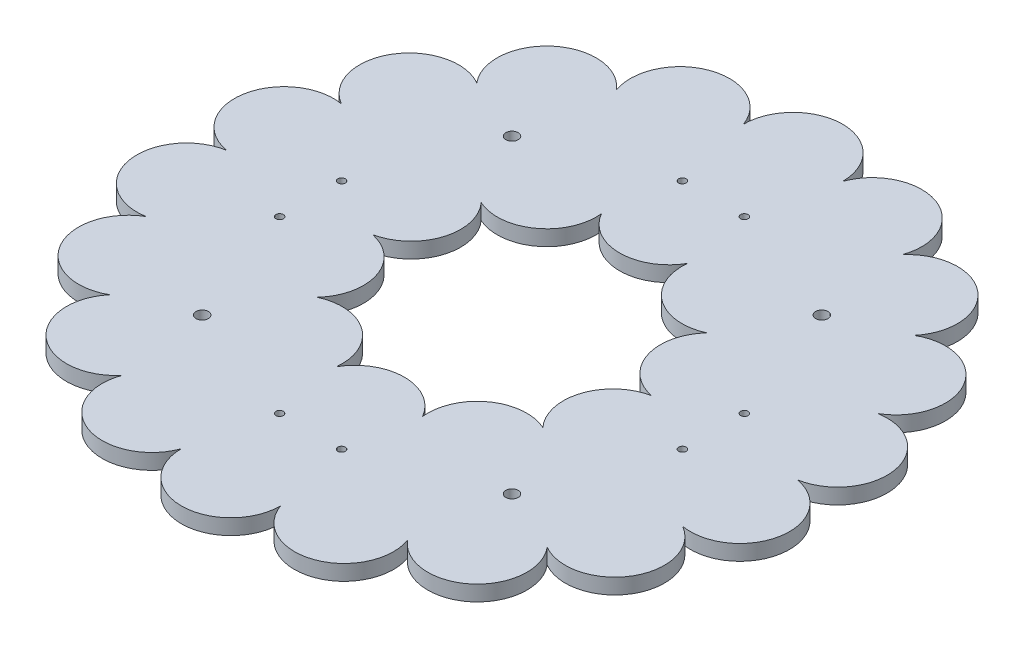
SolidWorks part; units mm, degrees
ref_plane "Front Plane" through (0, 0, 0) normal (0, 0, 1) x (1, 0, 0)
ref_plane "Top Plane" through (0, 0, 0) normal (0, 1, 0) x (1, 0, 0)
ref_plane "Right Plane" through (0, 0, 0) normal (1, 0, 0) x (0, 0, -1)
sketch "Sketch1" plane through (0, 0, 0) normal (0, 1, 0) x (1, 0, 0)
  circle A0 centre (0, 0) radius 64.4026
  circle A1 centre (0, 0) radius 115.2026
  dimension "D1" = 50.8
  dimension "D2" = 128.8051
extrude "Boss-Extrude1" add sketch "Sketch1" along normal blind 6.35
sketch "Sketch2" plane through (0, 6.35, 0) normal (0, 1, 0) x (1, 0, 0)
  circle A0 centre (0, 64.4026) radius 20.32
  circle A1 centre (0, 0) radius 64.4026 construction
  circle A2 centre (0, 115.2026) radius 20.32
  circle A3 centre (0, 0) radius 115.2026 construction
  circle A4 centre (37.8549, 52.1028) radius 20.32
  circle A5 centre (61.2505, 19.9015) radius 20.32
  circle A6 centre (61.2505, -19.9015) radius 20.32
  circle A7 centre (37.8549, -52.1028) radius 20.32
  circle A8 centre (0, -64.4026) radius 20.32
  circle A9 centre (-37.8549, -52.1028) radius 20.32
  circle A10 centre (-61.2505, -19.9015) radius 20.32
  circle A11 centre (-61.2505, 19.9015) radius 20.32
  circle A12 centre (-37.8549, 52.1028) radius 20.32
  circle A13 centre (39.4016, 108.255) radius 20.32
  circle A14 centre (74.0508, 88.2503) radius 20.32
  circle A15 centre (99.7683, 57.6013) radius 20.32
  circle A16 centre (113.4524, 20.0047) radius 20.32
  circle A17 centre (113.4524, -20.0047) radius 20.32
  circle A18 centre (99.7683, -57.6013) radius 20.32
  circle A19 centre (74.0508, -88.2503) radius 20.32
  circle A20 centre (39.4016, -108.255) radius 20.32
  circle A21 centre (0, -115.2026) radius 20.32
  circle A22 centre (-39.4016, -108.255) radius 20.32
  circle A23 centre (-74.0508, -88.2503) radius 20.32
  circle A24 centre (-99.7683, -57.6013) radius 20.32
  circle A25 centre (-113.4524, -20.0047) radius 20.32
  circle A26 centre (-113.4524, 20.0047) radius 20.32
  circle A27 centre (-99.7683, 57.6013) radius 20.32
  circle A28 centre (-74.0508, 88.2503) radius 20.32
  circle A29 centre (-39.4016, 108.255) radius 20.32
  point P28 (0, 0)
  point P63 (0, 0)
  dimension "D1" = 10
  dimension "D2" = 18
extrude "Boss-Extrude2" add sketch "Sketch2" against normal blind 6.35 contours A27 | A26 | A25 | A24 | A23 | A22 | A21 | A20 | A19 | A18 | A17 | A16 | A15 | A14 | A13 | A2 | A29 | A28 | A12 | A11 | A10 | A9 | A8 | A7 | A6 | A5 | A4 | A0
sketch "Sketch3" plane through (0, 6.35, 0) normal (0, 1, 0) x (1, 0, 0)
  line L0 (0, 129.8664) -> (0, -102.5368) construction
  line L1 (-99.5865, 0) -> (89.4092, 0) construction
  circle A0 centre (-63.5, 63.5) radius 2.54
  circle A1 centre (-63.5, -63.5) radius 2.54
  circle A2 centre (63.5, 63.5) radius 2.54
  circle A3 centre (63.5, -63.5) radius 2.54
  circle A4 centre (-12.7, 82.55) radius 1.524
  circle A5 centre (12.7, 82.55) radius 1.524
  circle A6 centre (82.55, 12.7) radius 1.524
  circle A7 centre (82.55, -12.7) radius 1.524
  circle A8 centre (12.7, -82.55) radius 1.524
  circle A9 centre (-12.7, -82.55) radius 1.524
  circle A10 centre (-82.55, -12.7) radius 1.524
  circle A11 centre (-82.55, 12.7) radius 1.524
  point P17 (-46.2334, 53.5552)
  point P18 (0, 0)
  point P32 (0, 0)
  dimension "D1" = 63.5
  dimension "D3" = 5.08
  dimension "D6" = 3.048
  dimension "D2" = 63.5
  dimension "D4" = 19.05
  dimension "D5" = 12.7
  dimension "D7" = 4
extrude "Cut-Extrude1" cut sketch "Sketch3" against normal through all
